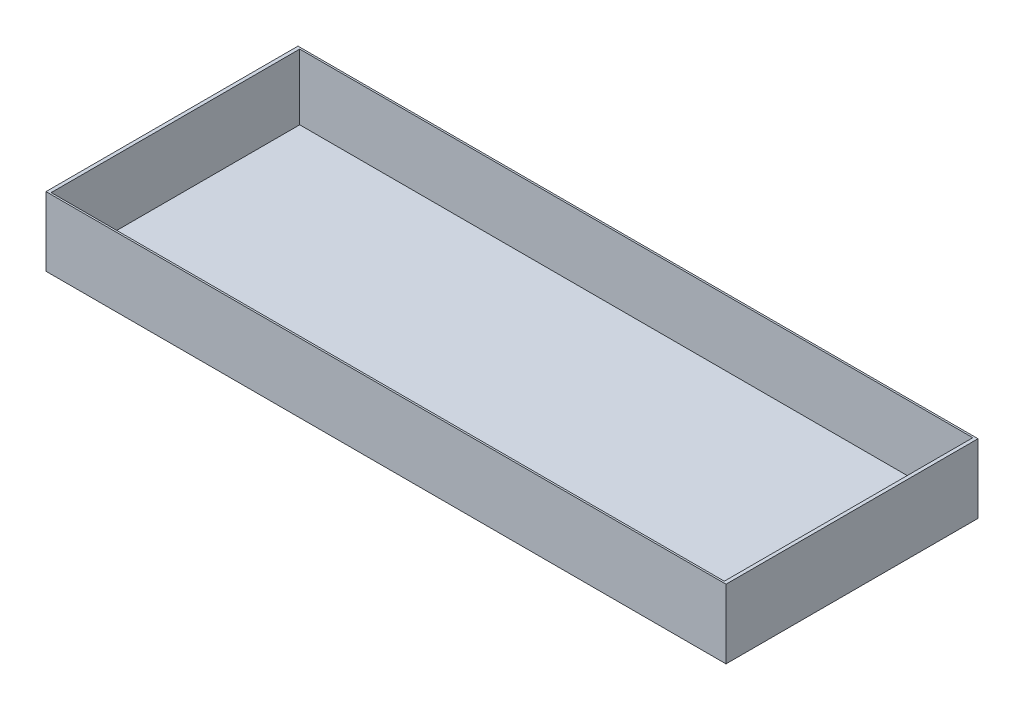
SolidWorks part; units mm, degrees
ref_plane "Front Plane" through (0, 0, 0) normal (0, 0, 1) x (1, 0, 0)
ref_plane "Top Plane" through (0, 0, 0) normal (0, 1, 0) x (1, 0, 0)
ref_plane "Right Plane" through (0, 0, 0) normal (1, 0, 0) x (0, 0, -1)
sketch "Sketch1" plane through (0, 0, 0) normal (0, 1, 0) x (1, 0, 0)
  line L1 (-98.5, 36.5) -> (98.5, 36.5)
  line L2 (-98.5, 36.5) -> (-98.5, -36.5)
  line L3 (-98.5, -36.5) -> (98.5, -36.5)
  line L4 (98.5, 36.5) -> (98.5, -36.5)
  line L5 (-98.5, 36.5) -> (98.5, -36.5) construction
  line L6 (-98.5, -36.5) -> (98.5, 36.5) construction
  point P0 (0, 0)
  dimension "D1" = 197
  dimension "D2" = 73
extrude "Boss-Extrude1" add sketch "Sketch1" along normal blind 20
sketch "Sketch2" plane through (0, 20, 0) normal (0, 1, 0) x (1, 0, 0)
  line L1 (-97.5, 36) -> (97.5, 36)
  line L2 (-97.5, 36) -> (-97.5, -36)
  line L3 (-97.5, -36) -> (97.5, -36)
  line L4 (97.5, 36) -> (97.5, -36)
  line L5 (-97.5, 36) -> (97.5, -36) construction
  line L6 (-97.5, -36) -> (97.5, 36) construction
  point P0 (0, 0)
  dimension "D1" = 72
  dimension "D2" = 195
extrude "Cut-Extrude1" cut sketch "Sketch2" against normal blind 19
